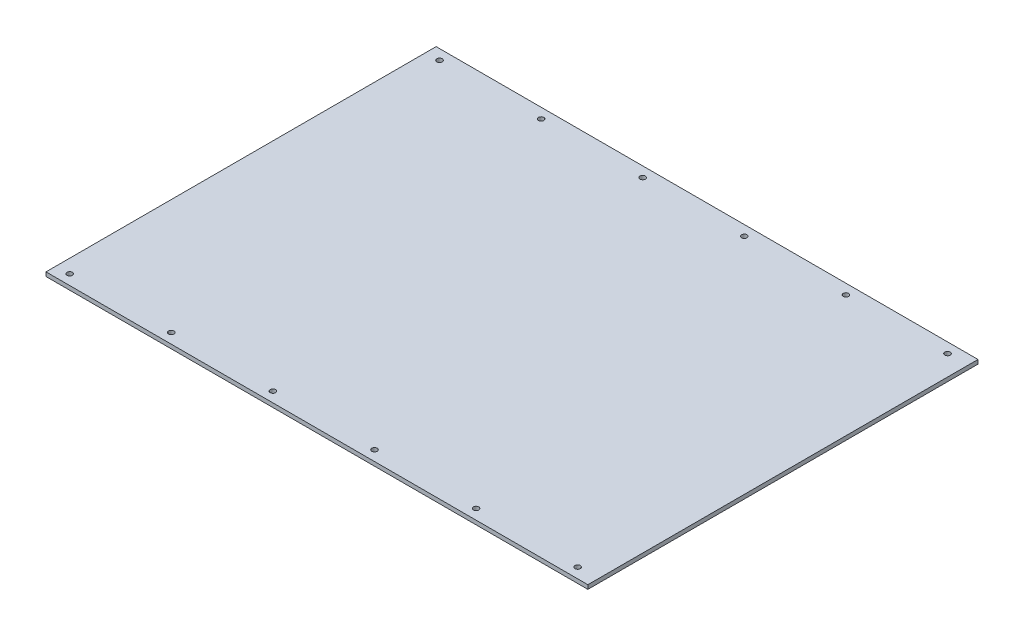
SolidWorks part; units mm, degrees
ref_plane "Front Plane" through (0, 0, 0) normal (0, 0, 1) x (1, 0, 0)
ref_plane "Top Plane" through (0, 0, 0) normal (0, 1, 0) x (1, 0, 0)
ref_plane "Right Plane" through (0, 0, 0) normal (1, 0, 0) x (0, 0, -1)
sketch "Sketch1" plane through (0, 0, 0) normal (0, 1, 0) x (1, 0, 0)
  line L1 (200, -144) -> (-200, -144)
  line L2 (200, -144) -> (200, 144)
  line L3 (200, 144) -> (-200, 144)
  line L4 (-200, -144) -> (-200, 144)
  line L5 (200, -144) -> (-200, 144) construction
  line L6 (200, 144) -> (-200, -144) construction
  point P0 (0, 0)
  dimension "D1" = 288
  dimension "D2" = 400
extrude "Boss-Extrude1" add sketch "Sketch1" along normal blind 3
sketch "Sketch2" plane through (0, 3, 0) normal (0, 1, 0) x (1, 0, 0)
  line L0 (200, 144) -> (-200, 144) construction
  line L1 (-200, 144) -> (-200, -144) construction
  line L2 (-55, 0) -> (55, 0) construction
  circle A0 centre (-190, 136.5) radius 2
  circle A1 centre (-115, 136.5) radius 2
  circle A2 centre (-40, 136.5) radius 2
  circle A3 centre (35, 136.5) radius 2
  circle A4 centre (110, 136.5) radius 2
  circle A5 centre (185, 136.5) radius 2
  circle A6 centre (185, -136.5) radius 2
  circle A7 centre (110, -136.5) radius 2
  circle A8 centre (35, -136.5) radius 2
  circle A9 centre (-40, -136.5) radius 2
  circle A10 centre (-115, -136.5) radius 2
  circle A11 centre (-190, -136.5) radius 2
  dimension "D1" = 7.5
  dimension "D2" = 10
  dimension "D4" = 75
  dimension "D3" = 6
extrude "Cut-Extrude1" cut sketch "Sketch2" against normal blind 10
